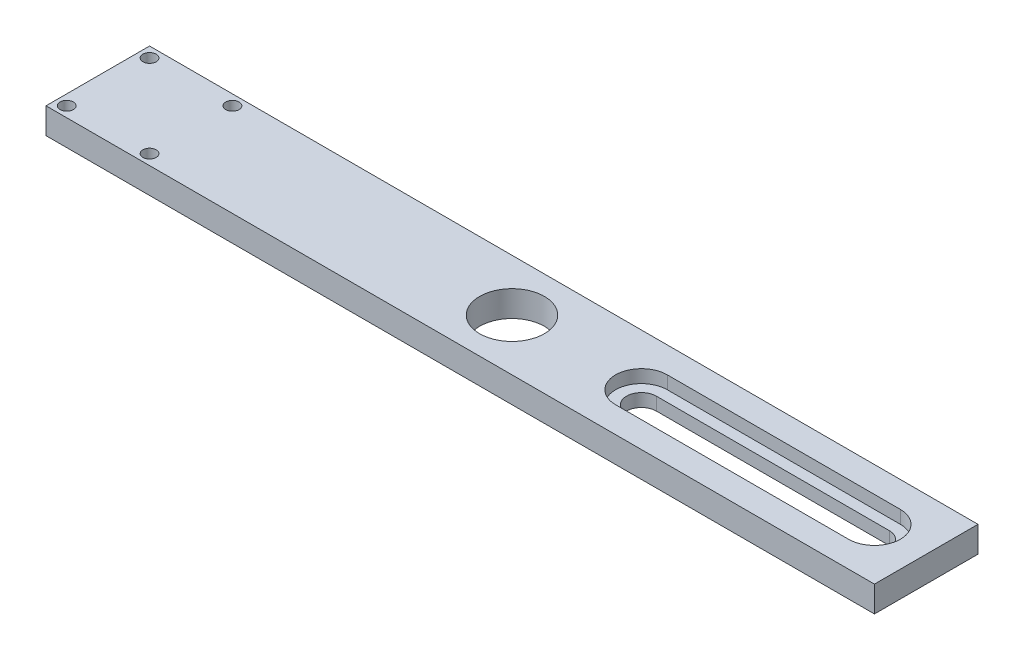
SolidWorks part; units mm, degrees
material "6061 Alloy"
ref_plane "Front Plane" through (0, 0, 0) normal (0, 0, 1) x (1, 0, 0)
ref_plane "Top Plane" through (0, 0, 0) normal (0, 1, 0) x (1, 0, 0)
ref_plane "Right Plane" through (0, 0, 0) normal (1, 0, 0) x (0, 0, -1)
sketch "Sketch1" plane through (0, 0, 0) normal (0, 1, 0) x (1, 0, 0)
  line L1 (0, 0) -> (203.2, 0)
  line L2 (0, 0) -> (0, 25.4)
  line L3 (0, 25.4) -> (203.2, 25.4)
  line L4 (203.2, 0) -> (203.2, 25.4)
  dimension "D1" = 203.2
  dimension "D2" = 25.4
extrude "Boss-Extrude1" add sketch "Sketch1" along normal blind 6.35
hole_wizard "5/8 (0.625) Diameter Hole1" positions "Sketch5" profile "Sketch4" hole size "5/8" standard "ANSI Inch"
sketch "Sketch5" plane through (0, 6.35, 0) normal (0, 1, 0) x (1, 0, 0)
  line L0 (203.2, 25.4) -> (0, 25.4) construction
  line L1 (203.2, 0) -> (203.2, 25.4) construction
  point P0 (101.6, 12.7)
  point P5 (101.6, 25.4)
  point P9 (203.2, 12.7)
sketch "Sketch4" plane through (101.6, 6.35, -12.7) normal (1, 0, 0) x (0, 0, 1)
  line L0 (0, 0) -> (0, 30.1693)
  line L1 (0, 30.1693) -> (7.9375, 25.4)
  line L2 (7.9375, 25.4) -> (7.9375, 0)
  line L5 (7.9375, 0) -> (0, 0)
  line L10 (0, 30.1693) -> (-7.9375, 25.4) construction
  line L11 (0, -6.35) -> (0, 107.95) construction
  dimension "Hole Dia." = 15.875
  dimension "Hole Depth" = 25.4
  dimension "Drill Angle" = 118
sketch "Sketch6" plane through (0, 6.35, 0) normal (0, 1, 0) x (1, 0, 0)
  line L0 (133.35, 12.7) -> (190.5, 12.7) construction
  line L1 (133.35, 16.3576) -> (190.5, 16.3576)
  line L2 (133.35, 9.0424) -> (190.5, 9.0424)
  line L3 (203.2, 0) -> (203.2, 25.4) construction
  arc A0 (133.35, 16.3576) -> (133.35, 9.0424) centre (133.35, 12.7) ccw
  arc A1 (190.5, 9.0424) -> (190.5, 16.3576) centre (190.5, 12.7) ccw
  point P2 (161.925, 12.7)
  point P9 (203.2, 12.7)
  dimension "D1" = 3.6576
  dimension "D2" = 12.7
  dimension "D3" = 69.85
extrude "Cut-Extrude1" cut sketch "Sketch6" against normal through all
sketch "Sketch7" plane through (0, 6.35, 0) normal (0, 1, 0) x (1, 0, 0)
  line L0 (190.5, 12.7) -> (133.35, 12.7) construction
  line L1 (190.5, 6.35) -> (133.35, 6.35)
  line L2 (190.5, 19.05) -> (133.35, 19.05)
  line L3 (203.2, 0) -> (203.2, 25.4) construction
  arc A0 (190.5, 6.35) -> (190.5, 19.05) centre (190.5, 12.7) ccw
  arc A1 (133.35, 19.05) -> (133.35, 6.35) centre (133.35, 12.7) ccw
  point P2 (161.925, 12.7)
  point P9 (203.2, 12.7)
  dimension "D1" = 6.35
  dimension "D2" = 12.7
  dimension "D3" = 69.85
extrude "Cut-Extrude2" cut sketch "Sketch7" against normal blind 3.175
hole_wizard "#4 Clearance Hole1" positions "Sketch9" profile "Sketch8" hole size "#4" standard "ANSI Inch" end condition through all
sketch "Sketch9" plane through (0, 6.35, 0) normal (0, 1, 0) x (1, 0, 0)
  line L0 (203.2, 25.4) -> (0, 25.4) construction
  line L1 (0, 0) -> (203.2, 0) construction
  line L2 (0, 25.4) -> (0, 0) construction
  point P0 (2.54, 22.86)
  point P2 (22.86, 22.86)
  point P4 (22.86, 2.54)
  point P6 (2.54, 2.54)
  dimension "D1" = 2.54
  dimension "D2" = 2.54
  dimension "D3" = 2.54
  dimension "D4" = 22.86
sketch "Sketch8" plane through (2.54, 6.35, -22.86) normal (1, 0, 0) x (0, 0, 1)
  line L0 (0, 0) -> (0, 6.35)
  line L1 (0, 6.35) -> (1.6319, 6.35)
  line L2 (1.6319, 6.35) -> (1.6319, 0)
  line L5 (1.6319, 0) -> (0, 0)
  line L11 (0, -6.35) -> (0, 107.95) construction
  dimension "Thru Hole Dia." = 3.2639
  dimension "Thru Hole Depth" = 6.35
